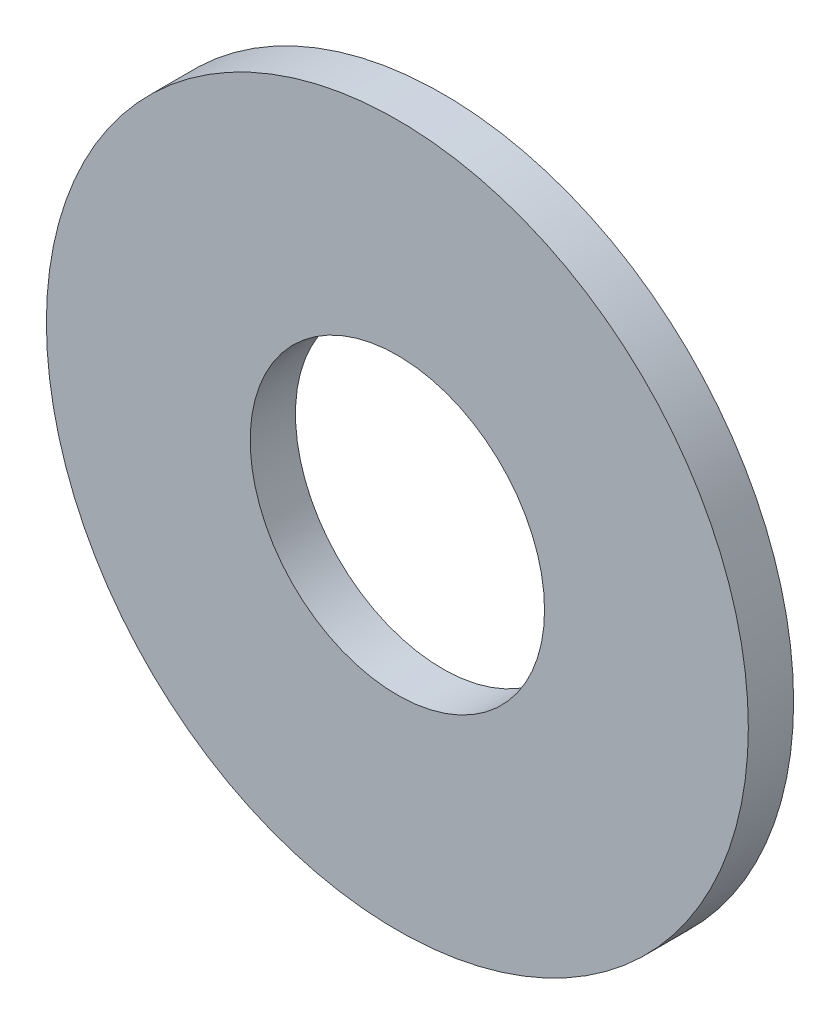
SolidWorks part; units mm, degrees
ref_plane "Front Plane" through (0, 0, 0) normal (0, 0, 1) x (1, 0, 0)
ref_plane "Top Plane" through (0, 0, 0) normal (0, 1, 0) x (1, 0, 0)
ref_plane "Right Plane" through (0, 0, 0) normal (1, 0, 0) x (0, 0, -1)
sketch "Sketch1" plane through (0, 0, 0) normal (0, 0, 1) x (1, 0, 0)
  line L0 (0, 0) -> (-74.9399, 0) construction
  circle A0 centre (0, 0) radius 49.2125
  circle A2 centre (0, 0) radius 35.6018 construction
  circle A3 centre (0, 0) radius 20.6375
  dimension "D1" = 98.425
  dimension "D2" = 13.6107
  dimension "D4" = 41.275
extrude "Boss-Extrude1" add sketch "Sketch1" along normal blind 6.35
